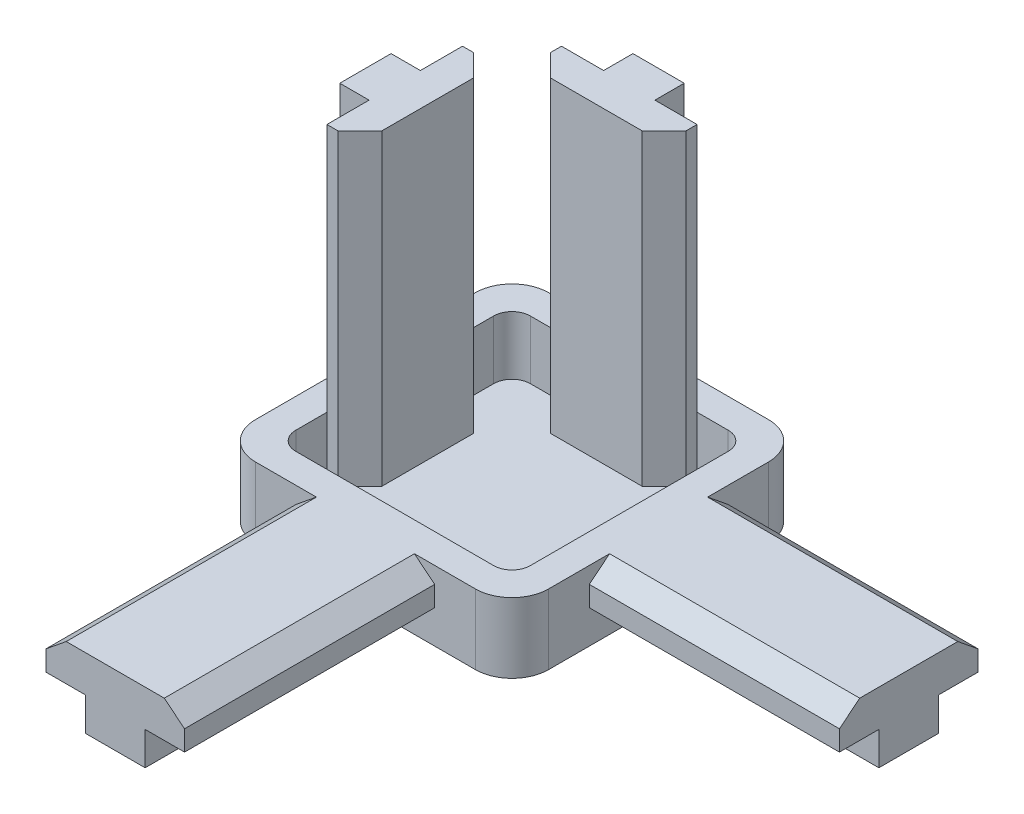
SolidWorks part; units mm, degrees
material "6061-T6 (SS)"
ref_plane "Front Plane" through (0, 0, 0) normal (0, 0, 1) x (1, 0, 0)
ref_plane "Top Plane" through (0, 0, 0) normal (0, 1, 0) x (1, 0, 0)
ref_plane "Right Plane" through (0, 0, 0) normal (1, 0, 0) x (0, 0, -1)
sketch "Sketch1" plane through (0, 0, 0) normal (0, 1, 0) x (1, 0, 0)
  line L1 (-20, 20) -> (20, 20)
  line L2 (-20, 20) -> (-20, -20)
  line L3 (-20, -20) -> (20, -20)
  line L4 (20, 20) -> (20, -20)
  line L5 (-20, 20) -> (20, -20) construction
  line L6 (-20, -20) -> (20, 20) construction
  point P0 (0, 0)
  dimension "D1" = 40
extrude "Boss-Extrude2" add sketch "Sketch1" along normal blind 9.54
sketch "Sketch2" plane through (0, 9.54, 0) normal (0, 1, 0) x (1, 0, 0)
  line L0 (20, 20) -> (-20, 20) construction
  line L1 (-16, -16) -> (16, -16)
  line L2 (-16, -16) -> (-16, 16)
  line L3 (-16, 16) -> (16, 16)
  line L4 (16, -16) -> (16, 16)
  line L5 (-16, -16) -> (16, 16) construction
  line L6 (-16, 16) -> (16, -16) construction
  point P0 (0, 0)
  dimension "D1" = 4
extrude "Cut-Extrude1" cut sketch "Sketch2" against normal blind 8
sketch "Sketch3" plane through (0, 1.54, 0) normal (0, 1, 0) x (1, 0, 0)
  line L0 (0, 0) -> (0, 20) construction
  line L1 (20, 20) -> (-20, 20) construction
  line L2 (3.5, 20) -> (-3.5, 20)
  line L3 (-3.5, 20) -> (-3.5, 16)
  line L4 (16, 16) -> (-16, 16) construction
  line L5 (-3.5, 16) -> (-9.25, 16)
  line L6 (-9.25, 16) -> (-9.25, 14.4844)
  line L7 (-9.25, 14.4844) -> (-6.2656, 11.5)
  line L8 (-6.2656, 11.5) -> (6.2656, 11.5)
  line L9 (9.25, 14.4844) -> (6.2656, 11.5)
  line L10 (9.25, 16) -> (9.25, 14.4844)
  line L11 (3.5, 16) -> (9.25, 16)
  line L12 (3.5, 20) -> (3.5, 16)
  point P14 (0, 11.5)
  dimension "D1" = 3.5
  dimension "D2" = 5.75
  dimension "D3" = 1.5156
  dimension "D4" = 135
  dimension "D5" = 2.9844
extrude "Boss-Extrude3" add sketch "Sketch3" along normal blind 42
ref_axis "Axis1" through (0, -2.177, 0) along (0, 1, 0)
pattern_circular "CirPattern1" count 2 over 90 about axis through (0, 0, 0) along (0, 1, 0) of "Boss-Extrude3"
sketch "Sketch4" plane through (0, 0, 20) normal (0, 0, 1) x (1, 0, 0)
  line L0 (0, 0) -> (0, 9.54) construction
  line L1 (-20, 9.54) -> (20, 9.54) construction
  line L2 (-4.075, 0) -> (4.075, 0)
  line L3 (-20, 0) -> (20, 0) construction
  line L4 (4.075, 0) -> (4.075, 4.54)
  line L5 (4.075, 4.54) -> (9.45, 4.54)
  line L6 (9.45, 4.54) -> (9.45, 7.3)
  line L7 (9.45, 7.3) -> (6.6897, 9.54)
  line L8 (6.6897, 9.54) -> (-6.6897, 9.54)
  line L9 (-9.45, 7.3) -> (-6.6897, 9.54)
  line L10 (-9.45, 4.54) -> (-9.45, 7.3)
  line L11 (-4.075, 4.54) -> (-9.45, 4.54)
  line L12 (-4.075, 0) -> (-4.075, 4.54)
  dimension "D1" = 4.075
  dimension "D2" = 4.54
  dimension "D3" = 5.375
  dimension "D4" = 2.76
  dimension "D5" = 129.06
extrude "Boss-Extrude4" add sketch "Sketch4" along normal blind 34.13
pattern_circular "CirPattern2" count 2 over 90 about axis through (0, 0, 0) along (0, 1, 0) of "Boss-Extrude4"
fillet "Fillet1" radius 2.5 4 edges at (-16, 5.54, 16) (16, 5.54, 16) (16, 5.54, -16) (-16, 5.54, -16)
fillet "Fillet2" radius 5 4 edges at (20, 4.77, -20) (-20, 4.77, -20) (-20, 4.77, 20) (20, 4.77, 20)
